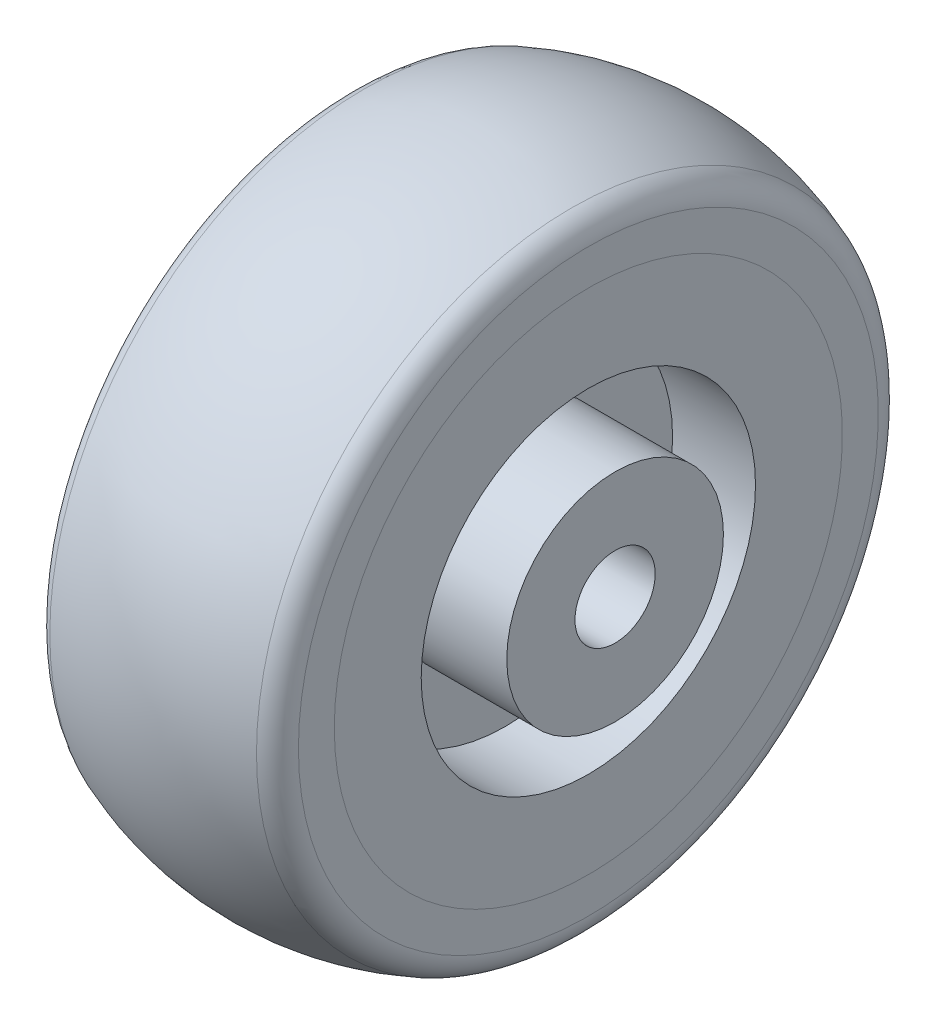
SolidWorks part; units mm, degrees
ref_plane "Plan de face" through (0, 0, 0) normal (0, 0, 1) x (1, 0, 0)
ref_plane "Plan de dessus" through (0, 0, 0) normal (0, 1, 0) x (1, 0, 0)
ref_plane "Plan de droite" through (0, 0, 0) normal (1, 0, 0) x (0, 0, -1)
sketch "Esquisse2" plane through (0, 0, 0) normal (0, 0, 1) x (1, 0, 0)
  line L0 (-11, 0) -> (11, 0) construction
  line L1 (-11, 3) -> (11, 3)
  line L2 (11, 3) -> (11, 8.1)
  line L3 (11, 8.1) -> (2.8, 8.1)
  line L4 (2.8, 8.1) -> (2.8, 12.5)
  line L5 (2.8, 12.5) -> (9, 12.5)
  line L6 (-2.8, 12.5) -> (-9, 12.5)
  line L7 (-9, 12.5) -> (-9, 21.6822)
  line L8 (9, 12.5) -> (9, 21.6822)
  line L9 (9, 23) -> (-9, 23) construction
  line L10 (-2.8, 12.5) -> (-2.8, 8.1)
  line L11 (-2.8, 8.1) -> (-11, 8.1)
  line L12 (-11, 8.1) -> (-11, 3)
  line L13 (0, 23) -> (0, 0) construction
  line L14 (0, 23) -> (0, 25) construction
  arc A0 (-7.7273, 23.5452) -> (7.7273, 23.5452) centre (0, 3.75) cw
  arc A1 (9, 21.6822) -> (7.7273, 23.5452) centre (7, 21.6822) ccw
  arc A2 (-9, 21.6822) -> (-7.7273, 23.5452) centre (-7, 21.6822) cw
  dimension "D8" = 50
  dimension "D9" = 2
  dimension "D1" = 22
  dimension "D2" = 6
  dimension "D3" = 16.2
  dimension "D4" = 6.2
  dimension "D5" = 25
  dimension "D6" = 18
  dimension "D7" = 2
revolve "Révolution1" add sketch "Esquisse2" angle 360 about L0
sketch "Esquisse3" plane through (9, 0, 0) normal (1, 0, 0) x (0, 0, -1)
  circle A0 centre (0, 0) radius 19
  dimension "D1" = 38
split line "Ligne de séparation1"
